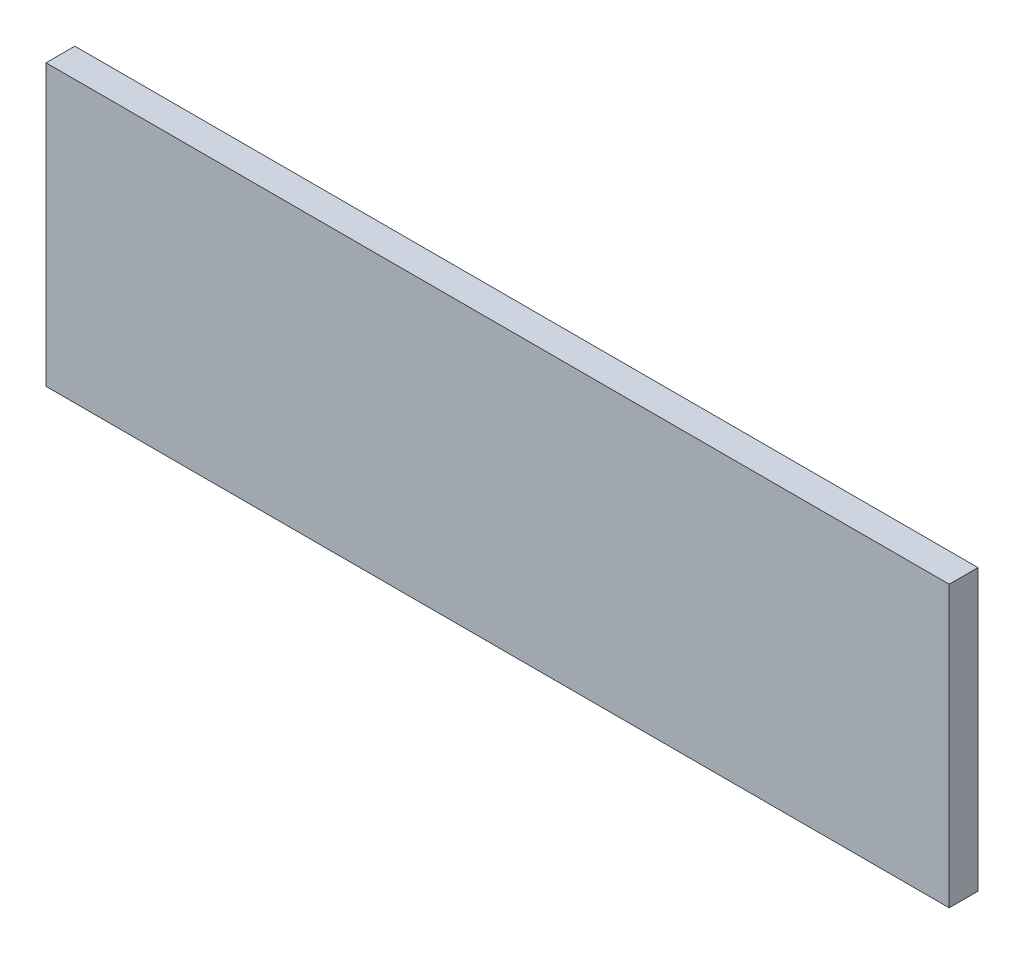
SolidWorks part; units mm, degrees
ref_plane "Front Plane" through (0, 0, 0) normal (0, 0, 1) x (1, 0, 0)
ref_plane "Top Plane" through (0, 0, 0) normal (0, 1, 0) x (1, 0, 0)
ref_plane "Right Plane" through (0, 0, 0) normal (1, 0, 0) x (0, 0, -1)
sketch "Sketch1" plane through (0, 0, 0) normal (0, 0, 1) x (1, 0, 0)
  line L1 (282, -87.5) -> (-282, -87.5)
  line L2 (282, -87.5) -> (282, 87.5)
  line L3 (282, 87.5) -> (-282, 87.5)
  line L4 (-282, -87.5) -> (-282, 87.5)
  line L5 (282, -87.5) -> (-282, 87.5) construction
  line L6 (282, 87.5) -> (-282, -87.5) construction
  point P0 (0, 0)
  dimension "D1" = 175
  dimension "D2" = 564
extrude "Boss-Extrude1" add sketch "Sketch1" along normal blind 18
equation "\"H_DSP\"=18"
equation "\"D1@Boss-Extrude1\"=\"H_DSP\""
equation "\"D2@Sketch1\"=600-2*\"H_DSP\""
